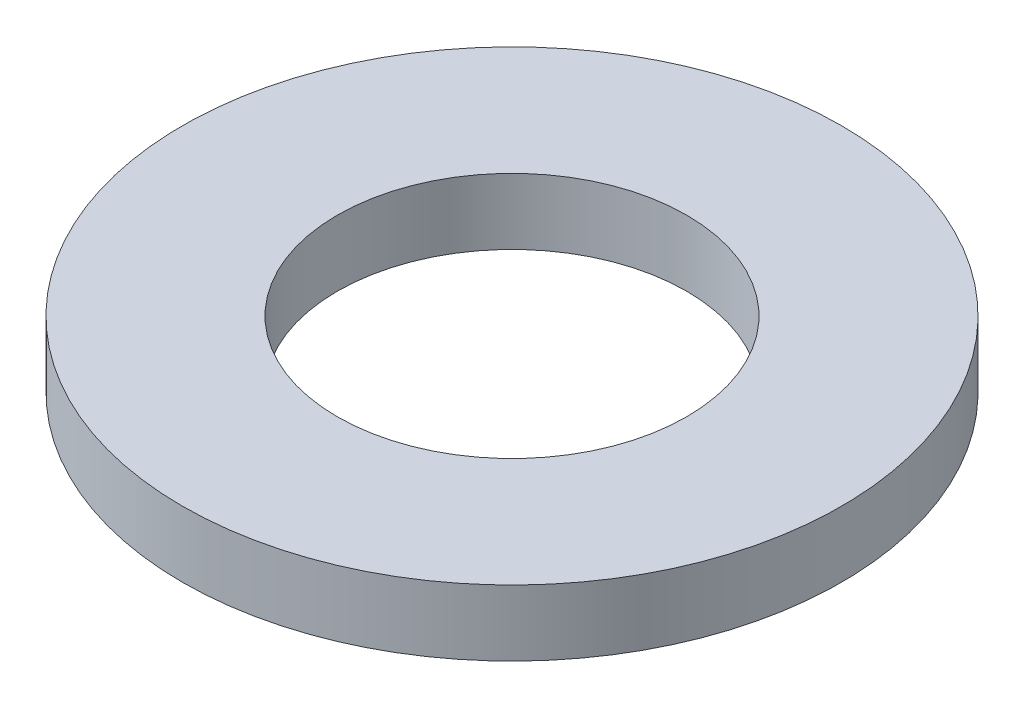
SolidWorks part; units mm, degrees
ref_plane "Front Plane" through (0, 0, 0) normal (0, 0, 1) x (1, 0, 0)
ref_plane "Top Plane" through (0, 0, 0) normal (0, 1, 0) x (1, 0, 0)
ref_plane "Right Plane" through (0, 0, 0) normal (1, 0, 0) x (0, 0, -1)
sketch "Sketch1" plane through (0, 0, 0) normal (0, 1, 0) x (1, 0, 0)
  circle A0 centre (0, 0) radius 5
  circle A1 centre (0, 0) radius 2.65
  dimension "D1" = 5.3
  dimension "D2" = 10
extrude "Boss-Extrude1" add sketch "Sketch1" along normal blind 1
